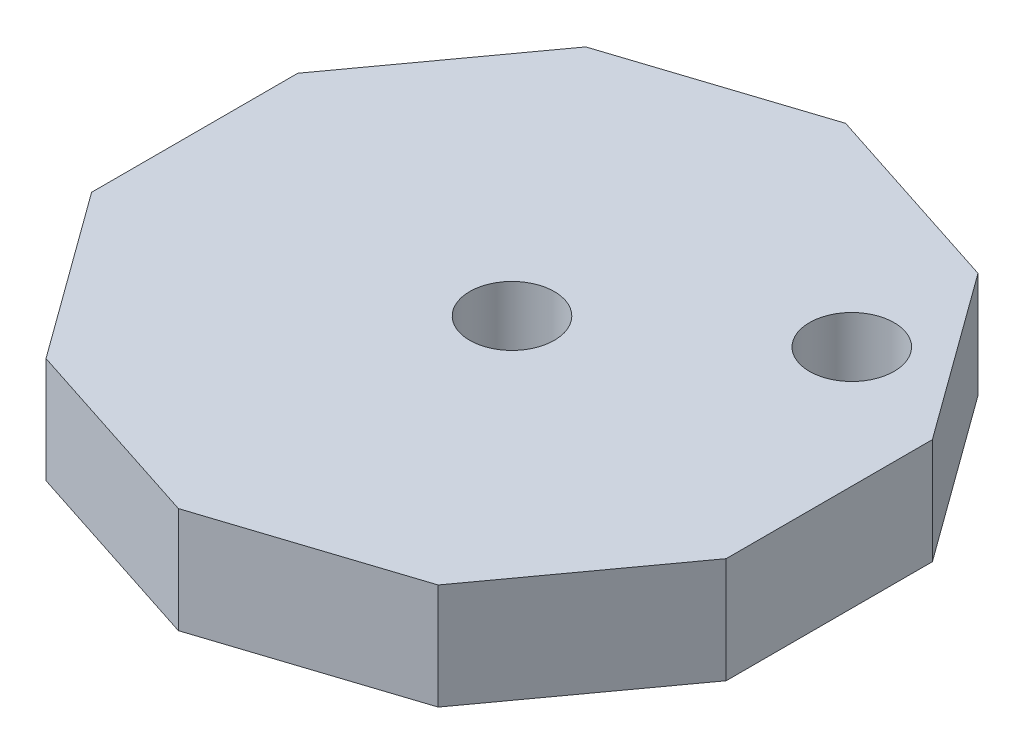
SolidWorks part; units mm, degrees
ref_plane "Front Plane" through (0, 0, 0) normal (0, 0, 1) x (1, 0, 0)
ref_plane "Top Plane" through (0, 0, 0) normal (0, 1, 0) x (1, 0, 0)
ref_plane "Right Plane" through (0, 0, 0) normal (1, 0, 0) x (0, 0, -1)
sketch "Sketch1" plane through (0, 0, 0) normal (0, 1, 0) x (1, 0, 0)
  line L0 (9.2705, -12.7598) -> (15, -4.8738)
  line L1 (0, 15.7719) -> (-9.2705, 12.7598)
  line L2 (-9.2705, 12.7598) -> (-15, 4.8738)
  line L3 (-15, 4.8738) -> (-15, -4.8738)
  line L4 (-15, -4.8738) -> (-9.2705, -12.7598)
  line L5 (-9.2705, -12.7598) -> (0, -15.7719)
  line L6 (0, -15.7719) -> (9.2705, -12.7598)
  line L7 (15, -4.8738) -> (15, 4.8738)
  line L8 (15, 4.8738) -> (9.2705, 12.7598)
  line L9 (9.2705, 12.7598) -> (0, 15.7719)
  circle A0 centre (0, 0) radius 15 construction
  dimension "D1" = 30
extrude "Boss-Extrude1" add sketch "Sketch1" along normal blind 5
sketch "Sketch2" plane through (0, 5, 0) normal (0, 1, 0) x (1, 0, 0)
  line L0 (12.1353, 8.8168) -> (0, 0) construction
  line L1 (15, 4.8738) -> (9.2705, 12.7598) construction
  circle A0 centre (0, 0) radius 2
  circle A1 centre (9.3037, 6.7595) radius 2
  dimension "D1" = 4
  dimension "D2" = 4
  dimension "D3" = 3.5
extrude "Cut-Extrude1" cut sketch "Sketch2" against normal blind 5 contours A1 L0 | L0 A1 | A0
